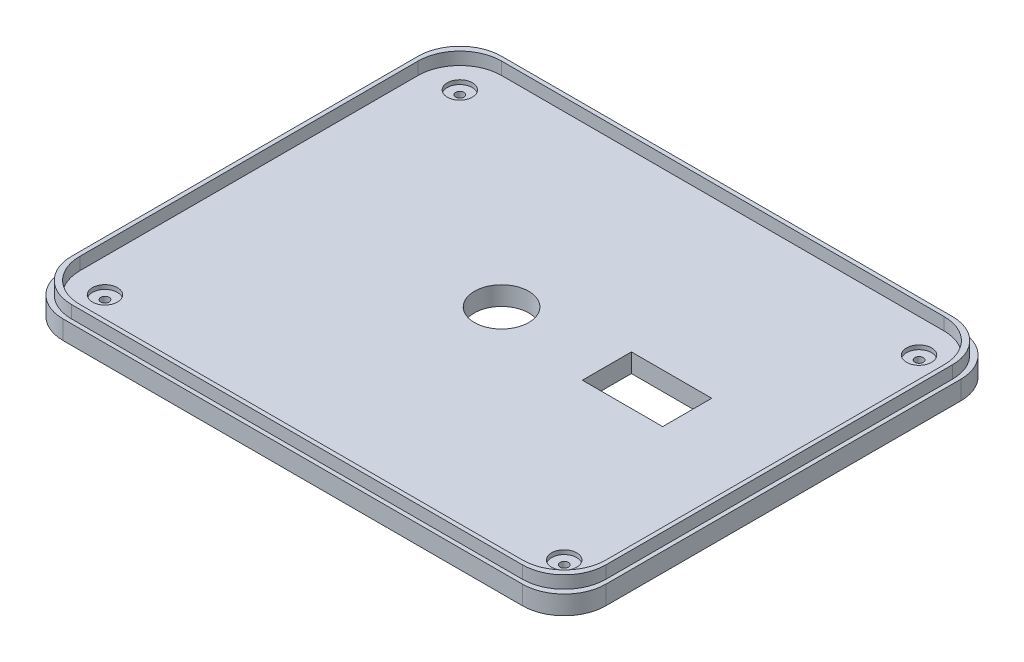
SolidWorks part; units mm, degrees
ref_plane "前视基准面" through (0, 0, 0) normal (0, 0, 1) x (1, 0, 0)
ref_plane "上视基准面" through (0, 0, 0) normal (0, 1, 0) x (1, 0, 0)
ref_plane "右视基准面" through (0, 0, 0) normal (1, 0, 0) x (0, 0, -1)
sketch "草图1" plane through (0, 0, 0) normal (0, 1, 0) x (1, 0, 0)
  line L1 (-50.4839, 65.4839) -> (59.5161, 65.4839)
  line L2 (-60.4839, 55.4839) -> (-60.4839, -29.5161)
  line L3 (-50.4839, -39.5161) -> (59.5161, -39.5161)
  line L4 (69.5161, 55.4839) -> (69.5161, -29.5161)
  circle A0 centre (-0.4839, 15.4839) radius 6.5
  arc A1 (59.5161, -39.5161) -> (69.5161, -29.5161) centre (59.5161, -29.5161) ccw
  arc A2 (59.5161, 65.4839) -> (69.5161, 55.4839) centre (59.5161, 55.4839) cw
  arc A3 (-60.4839, -29.5161) -> (-50.4839, -39.5161) centre (-50.4839, -29.5161) ccw
  arc A4 (-50.4839, 65.4839) -> (-60.4839, 55.4839) centre (-50.4839, 55.4839) ccw
  dimension "D5" = 13
  dimension "D6" = 10
  dimension "D1" = 130
  dimension "D2" = 105
  dimension "D3" = 70
  dimension "D4" = 55
extrude "凸台-拉伸1" add sketch "草图1" along normal blind 4.5
sketch "草图2" plane through (0, 4.5, 0) normal (0, 1, 0) x (1, 0, 0)
  line L0 (59.5161, 65.4839) -> (-50.4839, 65.4839) construction
  line L1 (-49.4839, 64.4839) -> (58.5161, 64.4839)
  line L2 (-59.4839, 54.4839) -> (-59.4839, -28.5161)
  line L3 (-49.4839, -38.5161) -> (58.5161, -38.5161)
  line L4 (68.5161, 54.4839) -> (68.5161, -28.5161)
  line L5 (-48.4839, 63.4839) -> (57.5161, 63.4839)
  line L6 (-58.4839, 53.4839) -> (-58.4839, -27.5161)
  line L7 (-48.4839, -37.5161) -> (57.5161, -37.5161)
  line L8 (67.5161, 53.4839) -> (67.5161, -27.5161)
  line L9 (69.5161, -29.5161) -> (69.5161, 55.4839) construction
  line L10 (-50.4839, -39.5161) -> (59.5161, -39.5161) construction
  line L11 (-60.4839, 55.4839) -> (-60.4839, -29.5161) construction
  arc A0 (-59.4839, -28.5161) -> (-49.4839, -38.5161) centre (-49.4839, -28.5161) ccw
  arc A1 (-58.4839, -27.5161) -> (-48.4839, -37.5161) centre (-48.4839, -27.5161) ccw
  arc A2 (58.5161, -38.5161) -> (68.5161, -28.5161) centre (58.5161, -28.5161) ccw
  arc A3 (57.5161, -37.5161) -> (67.5161, -27.5161) centre (57.5161, -27.5161) ccw
  arc A4 (58.5161, 64.4839) -> (68.5161, 54.4839) centre (58.5161, 54.4839) cw
  arc A5 (57.5161, 63.4839) -> (67.5161, 53.4839) centre (57.5161, 53.4839) cw
  arc A6 (-48.4839, 63.4839) -> (-58.4839, 53.4839) centre (-48.4839, 53.4839) ccw
  arc A7 (-49.4839, 64.4839) -> (-59.4839, 54.4839) centre (-49.4839, 54.4839) ccw
  dimension "D9" = 10
  dimension "D1" = 1
  dimension "D2" = 1
  dimension "D3" = 1
  dimension "D4" = 1
  dimension "D5" = 1
  dimension "D6" = 1
  dimension "D7" = 1
  dimension "D8" = 1
extrude "凸台-拉伸2" add sketch "草图2" along normal blind 3
sketch "草图3" plane through (0, 4.5, 0) normal (0, 1, 0) x (1, 0, 0)
  line L0 (-76.1772, 55.4839) -> (85.7247, 55.4839) construction
  line L1 (-78.4956, -29.5161) -> (83.1487, -29.5161) construction
  line L2 (-50.4839, 74.0996) -> (-50.4839, -48.3894) construction
  line L3 (59.5161, 74.0996) -> (59.5161, -45.5558) construction
  line L4 (69.5161, -29.5161) -> (69.5161, 55.4839) construction
  line L5 (-60.4839, 55.4839) -> (-60.4839, -29.5161) construction
  line L6 (59.5161, 65.4839) -> (-50.4839, 65.4839) construction
  line L7 (-50.4839, -39.5161) -> (59.5161, -39.5161) construction
  circle A0 centre (-50.4839, 55.4839) radius 1
  circle A1 centre (-50.4839, -29.5161) radius 1
  circle A2 centre (59.5161, -29.5161) radius 1
  circle A3 centre (59.5161, 55.4839) radius 1
  dimension "D5" = 2
  dimension "D6" = 2
  dimension "D7" = 2
  dimension "D8" = 2
  dimension "D1" = 10
  dimension "D2" = 10
  dimension "D3" = 10
  dimension "D4" = 10
extrude "切除-拉伸1" cut sketch "草图3" against normal blind 10
sketch "草图4" plane through (0, 4.5, 0) normal (0, 1, 0) x (1, 0, 0)
  circle A0 centre (-50.4839, 55.4839) radius 3
  circle A1 centre (59.5161, 55.4839) radius 3
  circle A2 centre (59.5161, -29.5161) radius 3
  circle A3 centre (-50.4839, -29.5161) radius 3
  dimension "D1" = 6
  dimension "D2" = 6
  dimension "D3" = 6
  dimension "D4" = 6
extrude "切除-拉伸2" cut sketch "草图4" against normal blind 1
sketch "草图5" plane through (0, 0, 0) normal (0, -1, 0) x (1, 0, 0)
  circle A0 centre (-50.4839, 29.5161) radius 3
  circle A1 centre (59.5161, 29.5161) radius 3
  circle A2 centre (59.5161, -55.4839) radius 3
  circle A3 centre (-50.4839, -55.4839) radius 3
  dimension "D1" = 6
  dimension "D2" = 6
  dimension "D3" = 6
  dimension "D4" = 6
extrude "切除-拉伸3" cut sketch "草图5" against normal blind 1.5
sketch "草图6" plane through (0, 4.5, 0) normal (0, 1, 0) x (1, 0, 0)
  line L0 (24.4004, 21.6994) -> (43.639, 21.6994)
  line L5 (24.4004, 21.6994) -> (24.4004, 9.9496)
  line L6 (24.4004, 9.9496) -> (43.639, 9.9496)
  line L7 (43.639, 21.6994) -> (43.639, 9.9496)
extrude "切除-拉伸6" cut sketch "草图6" against normal blind 10
